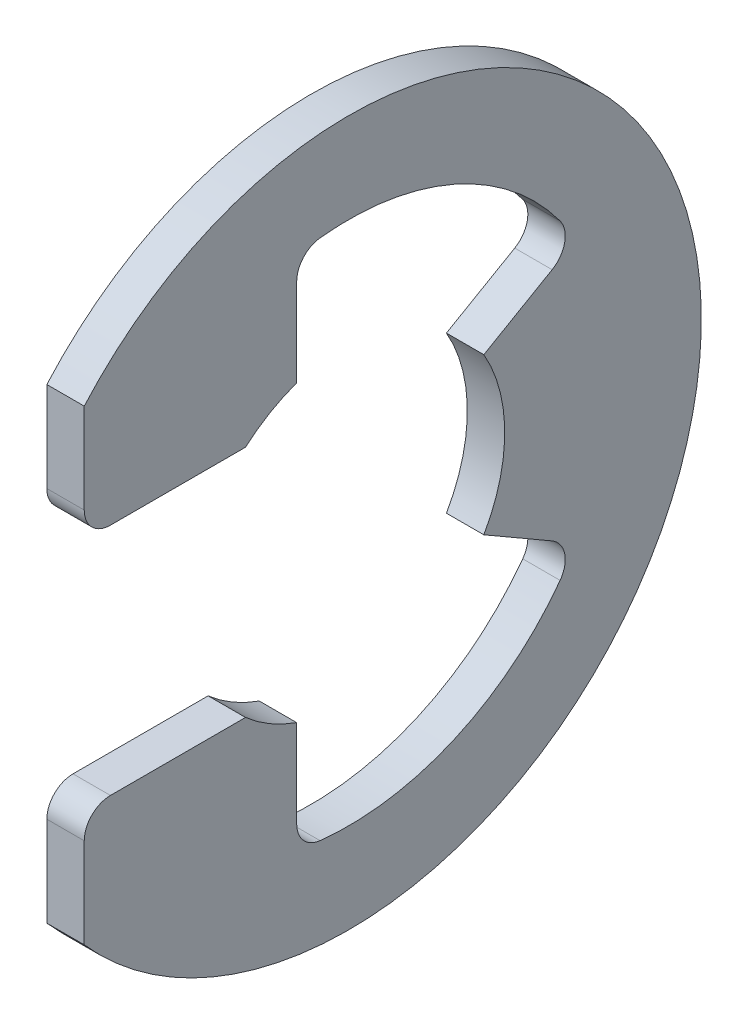
SolidWorks part; units mm, degrees
material "Cast Alloy Steel"
ref_plane "Front" through (0, 0, 0) normal (0, 0, 1) x (1, 0, 0)
ref_plane "Top" through (0, 0, 0) normal (0, 1, 0) x (1, 0, 0)
ref_plane "Right" through (0, 0, 0) normal (1, 0, 0) x (0, 0, -1)
sketch "Sketch1" plane through (0, 0, 0) normal (1, 0, 0) x (0, 0, -1)
  line L0 (-2.4529, 2.7813) -> (-6.2865, 2.7813)
  line L1 (-6.2865, 5.5442) -> (-6.2865, 2.7813)
  line L2 (-6.2865, -5.5442) -> (-6.2865, -2.7813)
  line L3 (-6.2865, -2.7813) -> (-2.4529, -2.7813)
  line L4 (3.2116, -1.8542) -> (5.4042, -3.1201)
  line L5 (3.2116, 1.8542) -> (5.4042, 3.1201)
  line L6 (0, 0) -> (-8.636, 0) construction
  line L7 (3.2116, 1.8542) -> (3.2116, -1.8542) construction
  line L8 (-1.2361, -3.4963) -> (-1.2361, -6.1165)
  line L9 (0, 8.382) -> (0, -8.382) construction
  line L10 (-1.2361, 6.1165) -> (-1.2361, 3.4963)
  circle A1 centre (0, 0) radius 8.636 construction
  circle A2 centre (0, 0) radius 3.7084 construction
  arc A3 (-6.2865, -5.5442) -> (-6.2865, 5.5442) centre (0, 0) ccw
  arc A4 (-2.4529, -2.7813) -> (-1.2361, -3.4963) centre (0, 0) ccw
  arc A5 (-2.4529, 2.7813) -> (-1.2361, 3.4963) centre (0, 0) cw
  arc A6 (3.2116, 1.8542) -> (3.2116, -1.8542) centre (0, 0) cw
  arc A7 (-1.2361, -6.1165) -> (5.4042, -3.1201) centre (0, 0) ccw
  arc A8 (5.4042, 3.1201) -> (-1.2361, 6.1165) centre (0, 0) ccw
  dimension "D1" = 6.2402
  dimension "OD" = 16.764
  dimension "L" = 17.272
  dimension "D" = 7.4168
  dimension "D5" = 1.2361
  dimension "D2" = 60
  dimension "D3" = 5.5626
  dimension "D4" = 14.6685
extrude "Extrude1" add sketch "Sketch1" along normal mid plane 0.889
fillet "Fillet1" radius 0.6223 6 edges at (0, -3.1201, -5.4042) (0, 3.1201, -5.4042) (0, -2.7813, 6.2865) (0, -6.1165, 1.2361) (0, 2.7813, 6.2865) (0, 6.1165, 1.2361)
sketch "Sketch3" plane through (0, 0, 0) normal (0, 1, 0) x (1, 0, 0)
  line L0 (0.4953, 4.7625) -> (0.4953, 3.8481)
  line L1 (0.4953, 3.8481) -> (-0.4953, 3.8481)
  line L2 (-0.4953, 3.8481) -> (-0.4953, 4.7625)
  line L3 (-0.4953, 4.7625) -> (-6.9342, 4.7625)
  line L4 (2.9718, 0) -> (2.9718, 4.3053)
  line L5 (-6.9342, 4.7625) -> (-6.9342, 0)
  line L6 (-6.9342, 0) -> (2.9718, 0)
  line L8 (2.9718, 0) -> (2.9718, 4.7625) construction
  line L9 (2.9718, 4.7625) -> (0.4953, 4.7625) construction
  line L10 (2.9718, 0) -> (17.2631, 0) construction
  line L11 (2.9718, 4.3053) -> (2.5146, 4.7625)
  line L12 (2.5146, 4.7625) -> (0.4953, 4.7625)
  point P2 (0, 3.8481)
  point P5 (0.4953, 4.3053)
  dimension "D1" = 2.4765
  dimension "Ds" = 9.525
  dimension "Dg" = 7.6962
  dimension "W" = 0.9906
  dimension "D2" = 9.906
  dimension "D3" = 45
revolve "Revolve2" [suppressed] add sketch "Sketch3" angle 360 about L10
equation "\"D2@Sketch3\" = \"W@Sketch3\"*10"
equation "\"D1@Sketch3\" = \"D2@Sketch3\"/4"
equation "\"D1@Sketch1\" = (\"OD@Sketch1\"+\"D@Sketch1\")/3.875"
equation "\"D3@Sketch1\" = \"D@Sketch1\"*.75"
equation "\"D1@Fillet1\" = \"D1@Extrude1\"*.7"
equation "\"D4@Sketch1\" = \"OD@Sketch1\"*.875"
equation "\"D5@Sketch1\" = \"D@Sketch1\"/6"
